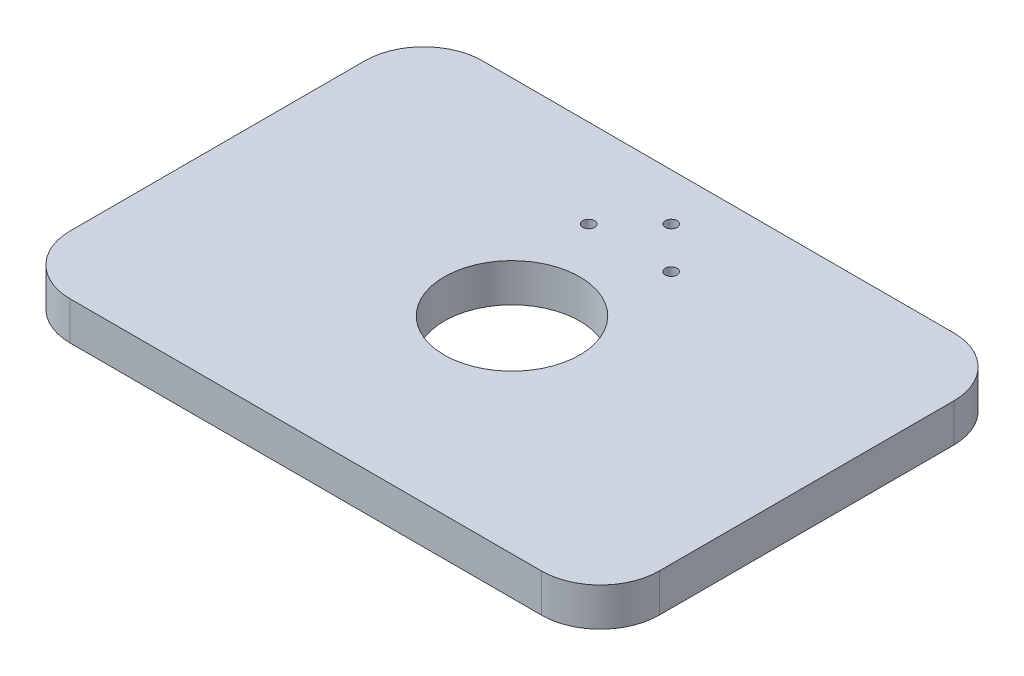
SolidWorks part; units mm, degrees
ref_plane "Front" through (0, 0, 0) normal (0, 0, 1) x (1, 0, 0)
ref_plane "Top" through (0, 0, 0) normal (0, 1, 0) x (1, 0, 0)
ref_plane "Right" through (0, 0, 0) normal (1, 0, 0) x (0, 0, -1)
sketch "Sketch1" plane through (0, 0, 0) normal (0, 1, 0) x (1, 0, 0)
  line L1 (50, -35) -> (-50, -35)
  line L2 (50, -35) -> (50, 35)
  line L3 (50, 35) -> (-50, 35)
  line L4 (-50, -35) -> (-50, 35)
  line L5 (50, -35) -> (-50, 35) construction
  line L6 (50, 35) -> (-50, -35) construction
  point P0 (0, 0)
  dimension "D1" = 100
  dimension "D2" = 70
extrude "Boss-Extrude1" add sketch "Sketch1" along normal blind 6.5
extrude "Cut-Extrude1" cut sketch "Sketch2" against normal blind 19 contours A0
sketch "Sketch2" plane through (10.2122, 6.5, 1.8424) normal (0, 1, 0) x (1, 0, 0)
  line L0 (-21.7122, 21.3424) -> (1.2878, -17.6576)
  line L1 (1.2878, 21.3424) -> (-21.7122, -17.6576)
  line L8 (1.2878, 21.3424) -> (-21.7122, 21.3424)
  line L9 (-21.7122, 21.3424) -> (-21.7122, -17.6576)
  line L10 (-21.7122, -17.6576) -> (1.2878, -17.6576)
  line L11 (1.2878, -17.6576) -> (1.2878, 21.3424)
  circle A0 centre (-10.2122, 1.8424) radius 11.5
  point P6 (-10.2122, 1.8424)
extrude "Cut-Extrude2" cut sketch "Sketch3" along normal blind 8
sketch "Sketch3" plane through (10.2122, 6.5, 1.8424) normal (0, -1, 0) x (1, 0, 0)
  arc A6 (-17.2122, -20.8724) -> (-17.2122, -22.8524) centre (-17.2122, -21.8624) ccw
  arc A7 (-17.2122, -22.8524) -> (-17.2122, -20.8724) centre (-17.2122, -21.8624) ccw
  arc A8 (-10.2122, -27.8624) -> (-10.2122, -29.8624) centre (-10.2122, -28.8624) ccw
  arc A9 (-10.2122, -29.8624) -> (-10.2122, -27.8624) centre (-10.2122, -28.8624) ccw
  arc A10 (-3.2122, -20.8624) -> (-3.2122, -22.8624) centre (-3.2122, -21.8624) ccw
  arc A11 (-3.2122, -22.8624) -> (-3.2122, -20.8624) centre (-3.2122, -21.8624) ccw
fillet "Fillet1" radius 10 4 edges at (-50, 3.25, -35) (-50, 3.25, 35) (50, 3.25, 35) (50, 3.25, -35)
